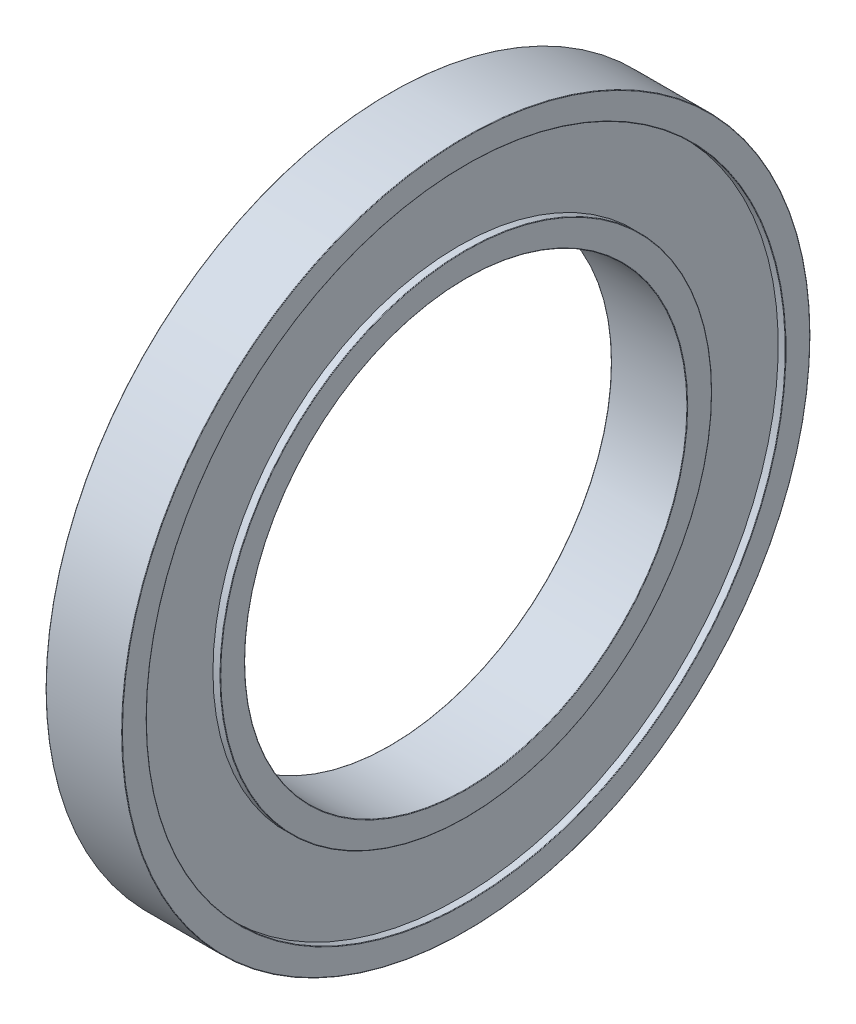
SolidWorks part; units mm, degrees
material "1.0161 Blank"
ref_plane "Ebene vorne" through (0, 0, 0) normal (0, 0, 1) x (1, 0, 0)
ref_plane "Ebene oben" through (0, 0, 0) normal (0, 1, 0) x (1, 0, 0)
ref_plane "Ebene rechts" through (0, 0, 0) normal (1, 0, 0) x (0, 0, -1)
sketch "Skizze1" plane through (0, 0, 0) normal (0, 0, 1) x (1, 0, 0)
  line L0 (0, 0) -> (31, 0) construction
  line L1 (0, 130) -> (0, 140)
  line L2 (0, 130) -> (3, 130)
  line L3 (3, 130) -> (3, 100)
  line L4 (3, 100) -> (0, 100)
  line L5 (0, 100) -> (0, 90)
  line L6 (0, 140) -> (31, 140)
  line L7 (31, 140) -> (31, 130)
  line L8 (31, 130) -> (28, 130)
  line L9 (28, 130) -> (28, 100)
  line L10 (28, 100) -> (31, 100)
  line L11 (31, 100) -> (31, 90)
  line L12 (31, 90) -> (0, 90)
  line L13 (15.5, 90) -> (15.5, 140) construction
  line L14 (3, 115) -> (28, 115) construction
  dimension "Innendurchmesser " = 180
  dimension "Außendurchmesser " = 280
  dimension "Breite " = 31
  dimension "Auflagefläche " = 10
  dimension "Auflagetiefe " = 3
revolve "Rotation1" add sketch "Skizze1" angle 360 about L0
fillet "Verrundung1" radius 0.2 8 edges at (0, 0, 100) (0, 0, 90) (31, 0, 90) (31, 0, 100) (31, 0, 130) (31, 0, 140) (0, 0, 140) (0, 0, 130)
other "PropertyManager"
